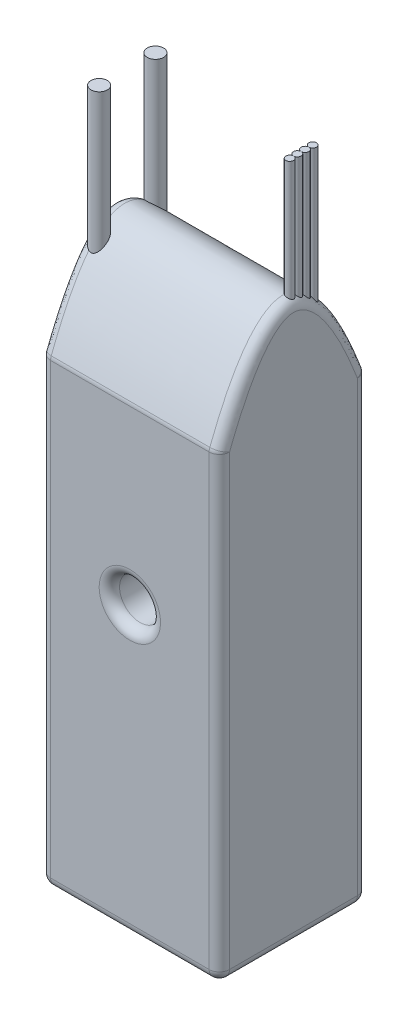
SolidWorks part; units mm, degrees
ref_plane "Front Plane" through (0, 0, 0) normal (0, 0, 1) x (1, 0, 0)
ref_plane "Top Plane" through (0, 0, 0) normal (0, 1, 0) x (1, 0, 0)
ref_plane "Right Plane" through (0, 0, 0) normal (1, 0, 0) x (0, 0, -1)
sketch "Sketch2" plane through (0, 0, 0) normal (0, 1, 0) x (1, 0, 0)
  line L1 (-17.5, 14.5) -> (17.5, 14.5)
  line L2 (-17.5, 14.5) -> (-17.5, -14.5)
  line L3 (-17.5, -14.5) -> (17.5, -14.5)
  line L4 (17.5, 14.5) -> (17.5, -14.5)
  line L5 (-17.5, 14.5) -> (17.5, -14.5) construction
  line L6 (-17.5, -14.5) -> (17.5, 14.5) construction
  point P0 (0, 0)
  dimension "D1" = 35
  dimension "D2" = 29
extrude "Boss-Extrude1" add sketch "Sketch2" along normal blind 109
sketch "Sketch3" plane through (17.5, 0, 0) normal (1, 0, 0) x (0, 0, -1)
  line L5 (-14.5, 109) -> (-14.5, 0) construction
  line L6 (-14.5, 109) -> (14.5, 109) construction
  line L7 (14.5, 109) -> (14.5, 0) construction
  line L16 (-14.5, 0) -> (14.5, 0)
  line L17 (14.5, 0) -> (14.5, 109)
  line L18 (14.5, 109) -> (-14.5, 109)
  line L19 (-14.5, 109) -> (-14.5, 0)
  line L20 (-14.5, 0) -> (14.5, 0)
  line L21 (14.5, 0) -> (14.5, 109)
  line L22 (14.5, 109) -> (-14.5, 109)
  line L23 (-14.5, 109) -> (-14.5, 0)
  spline S0 degree 2 poles (-14.5, 90) (0, 128) (14.5, 90) knots 0 0 0 1 1 1
  line M7 (14.5, 109) -> (-14.5, 109)
  line M8 (-14.5, 109) -> (-14.5, 0)
  dimension "D1" = 90
  dimension "D2" = 0
extrude "Cut-Extrude1" cut sketch "Sketch3" against normal up to surface (35 mm away) contours S0 L21 M7 | S0 L22 M8 up to face at (-17.5, 54.5, 0)
sketch "Sketch4" plane through (0, 0, 0) normal (0, -1, 0) x (1, 0, 0)
  line L0 (-17.5, 14.5) -> (-17.5, -14.5) construction
  line L1 (-17.5, -14.5) -> (17.5, -14.5) construction
  line L2 (-17.5, 0) -> (16, 0) construction
  line L5 (-17.5, -14.5) -> (-17.5, 14.5) construction
  line L6 (17.5, 14.5) -> (17.5, -14.5) construction
  circle A0 centre (-15, -5.5) radius 1.6
  circle A2 centre (-15, 5.5) radius 1.6
  circle A3 centre (16, -0.75) radius 0.75
  circle A4 centre (16, -2.25) radius 0.75
  circle A5 centre (16, -3.75) radius 0.75
  circle A6 centre (16, -5.25) radius 0.75
  dimension "D1" = 3.2
  dimension "D3" = 1.5
  dimension "D2" = 9
  dimension "D5" = 1.5
  dimension "D6" = 2.5
  dimension "D7" = 1.5
  dimension "D4" = 4
extrude "Boss-Extrude3" add sketch "Sketch4" against normal blind 130 from offset 2 separate body contours A0 | A2 | A6 | A5 | A4 | A3 offset against normal yes
fillet "Fillet1" radius 2 12 edges at (17.5, 45, -14.5) (0, 90, -14.5) (0, 0, -14.5) (17.5, 0, 0) (0, 0, 14.5) (0, 90, 14.5) (17.5, 45, 14.5) (-17.5, 0, 0) (-17.5, 45, -14.5) (-17.5, 45, 14.5)
sketch "Sketch5" plane through (0, 0, 14.5) normal (0, 0, 1) x (1, 0, 0)
  line L0 (15.5, 0) -> (-15.5, 0) construction
  circle A0 centre (0, 56) radius 4
  dimension "D2" = 8
  dimension "D1" = 56
extrude "Cut-Extrude2" cut sketch "Sketch5" against normal up to surface (29 mm away) up to face at (0, 45.8149, -14.5)
fillet "Fillet2" radius 2 2 edges at (4, 56, -14.5) (4, 56, 14.5)
